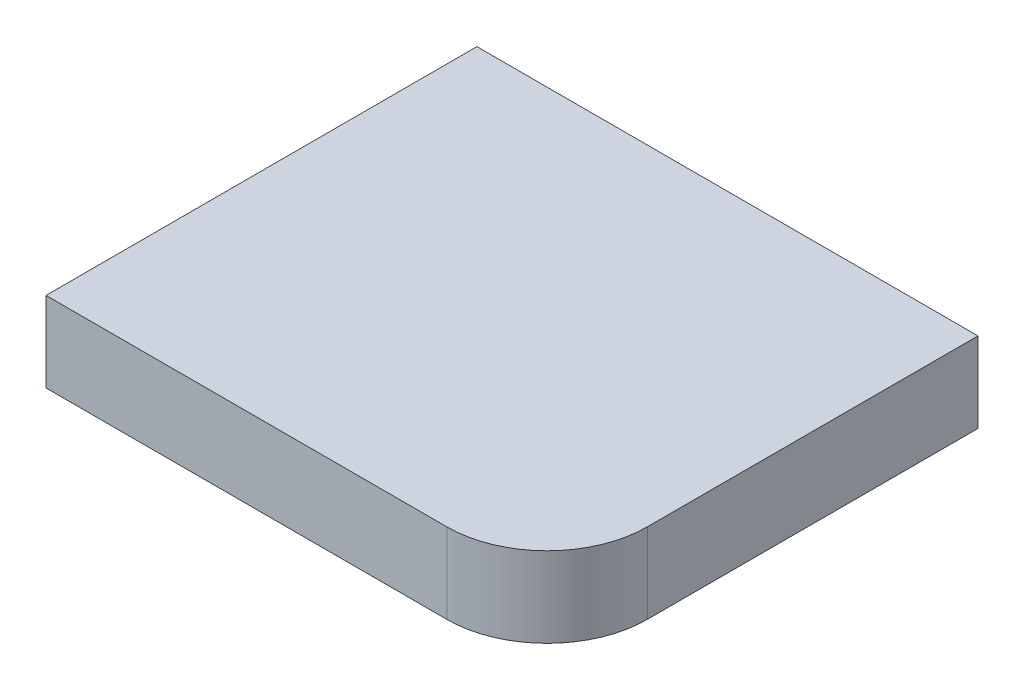
SolidWorks part; units mm, degrees
material "Клен"
ref_plane "Спереди" through (0, 0, 0) normal (0, 0, 1) x (1, 0, 0)
ref_plane "Сверху" through (0, 0, 0) normal (0, 1, 0) x (1, 0, 0)
ref_plane "Справа" through (0, 0, 0) normal (1, 0, 0) x (0, 0, -1)
sketch "Эскиз1" plane through (0, 0, 0) normal (0, 1, 0) x (1, 0, 0)
  line L1 (-25, -21.5) -> (15, -21.5)
  line L2 (-25, -21.5) -> (-25, 21.5)
  line L3 (-25, 21.5) -> (25, 21.5)
  line L4 (25, -11.5) -> (25, 21.5)
  line L5 (-25, -21.5) -> (25, 21.5) construction
  line L6 (-25, 21.5) -> (25, -21.5) construction
  arc A0 (15, -21.5) -> (25, -11.5) centre (15, -11.5) ccw
  point P0 (0, 0)
  dimension "D3" = 10
  dimension "D1" = 50
  dimension "D2" = 43
extrude "Бобышка-Вытянуть1" add sketch "Эскиз1" along normal blind 8
